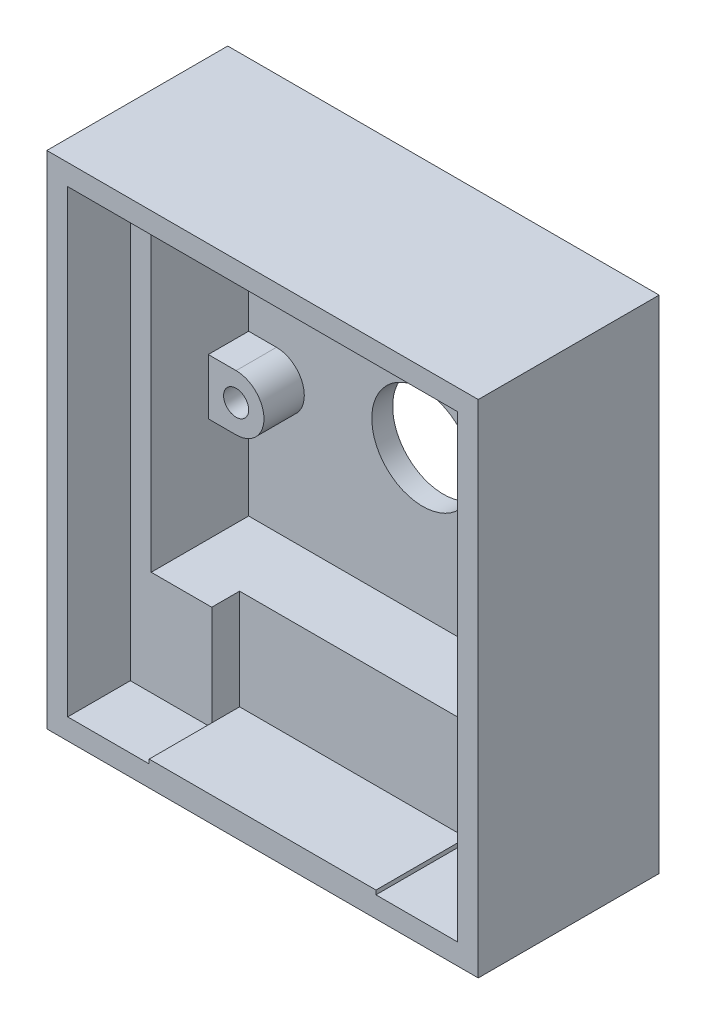
SolidWorks part; units mm, degrees
ref_plane "Alzado" through (0, 0, 0) normal (0, 0, 1) x (1, 0, 0)
ref_plane "Planta" through (0, 0, 0) normal (0, 1, 0) x (1, 0, 0)
ref_plane "Vista lateral" through (0, 0, 0) normal (1, 0, 0) x (0, 0, -1)
sketch "Croquis1" plane through (0, 0, 0) normal (0, 0, 1) x (1, 0, 0)
  line L1 (-4.65, -4.5) -> (4.65, -4.5) construction
  line L2 (-4.65, -4.5) -> (-4.65, 4.5) construction
  line L3 (-4.65, 4.5) -> (4.65, 4.5) construction
  line L4 (4.65, -4.5) -> (4.65, 4.5) construction
  line L5 (-4.65, -4.5) -> (4.65, 4.5) construction
  line L6 (-4.65, 4.5) -> (4.65, -4.5) construction
  line L7 (-12.5, -10.5) -> (12.5, -10.5)
  line L8 (-12.5, -10.5) -> (-12.5, 13.5)
  line L9 (-12.5, 13.5) -> (12.5, 13.5)
  line L10 (12.5, -10.5) -> (12.5, 13.5)
  circle A0 centre (0, 0) radius 3.65
  point P1 (0, 0)
  point P6 (0, 0)
  point P11 (0, 0)
  point P16 (0, 13.5)
  dimension "D6" = 7.3
  dimension "D1" = 25
  dimension "D2" = 9.3
  dimension "D3" = 9
  dimension "D4" = 6
  dimension "D5" = 24
extrude "Saliente-Extruir1" add sketch "Croquis1" along normal blind 1.5
sketch "Croquis4" plane through (0, 0, 0) normal (0, 0, -1) x (-1, 0, 0)
  line L0 (12.5, -10.5) -> (12.5, 13.5)
  line L1 (12.5, 13.5) -> (-12.5, 13.5)
  line L2 (-12.5, 13.5) -> (-12.5, -10.5)
  line L3 (-12.5, -10.5) -> (-15.5, -10.5)
  line L4 (-15.5, -10.5) -> (-15.5, 16.5)
  line L5 (-15.5, 16.5) -> (15.5, 16.5)
  line L6 (15.5, 16.5) -> (15.5, -10.5)
  line L7 (15.5, -10.5) -> (12.5, -10.5)
  dimension "D1" = 3
  dimension "D2" = 3
  dimension "D3" = 3
extrude "Saliente-Extruir7" add sketch "Croquis4" against normal blind 8.5
sketch "Croquis2" plane through (0, 0, 1.5) normal (0, 0, 1) x (1, 0, 0)
  line L2 (-12.5, 13.5) -> (-12.5, -10.5) construction
  line L3 (12.5, 13.5) -> (-12.5, 13.5) construction
  line L4 (-10.5, 9.5) -> (-12.5, 9.5)
  line L5 (-12.5, 13.5) -> (-12.5, -10.5) construction
  line L6 (-12.5, 9.5) -> (-12.5, 13.5)
  line L7 (-12.5, 13.5) -> (-10.5, 13.5)
  line L8 (-10.5, -3) -> (-12.5, -3)
  line L9 (-12.5, -3) -> (-12.5, 1)
  line L10 (-12.5, 1) -> (-10.5, 1)
  arc A0 (-10.5, 9.5) -> (-10.5, 13.5) centre (-10.5, 11.5) ccw
  arc A1 (-10.5, -3) -> (-10.5, 1) centre (-10.5, -1) ccw
  circle A2 centre (-10.5, 11.5) radius 0.9
  circle A3 centre (-10.5, -1) radius 0.9
  dimension "D1" = 4
  dimension "D2" = 1.8
  dimension "D3" = 2
  dimension "D4" = 2
  dimension "D5" = 12.5
extrude "Saliente-Extruir2" add sketch "Croquis2" along normal blind 2.9
mirror "Simetría2" about plane through (0, 0, 0) normal (1, 0, 0) of "Saliente-Extruir2"
sketch "Croquis5" plane through (0, 0, 0) normal (0, 0, -1) x (-1, 0, 0)
  line L0 (12.5, -10.5) -> (-12.5, -10.5) construction
  line L1 (8.15, -10.5) -> (-8.15, -10.5) construction
  line L2 (8.15, -10.5) -> (8.15, -16.2434) construction
  line L3 (8.15, -16.2434) -> (-8.15, -16.2434) construction
  line L4 (-8.15, -10.5) -> (-8.15, -16.2434) construction
  line L5 (-8.15, -10.5) -> (-8.15, -14.15)
  line L6 (-15.5, 16.5) -> (-15.5, -10.5) construction
  line L7 (15.5, -10.5) -> (-15.5, -10.5)
  line L8 (15.5, -10.5) -> (15.5, -19.5)
  line L9 (15.5, -19.5) -> (-15.5, -19.5)
  line L10 (-15.5, -10.5) -> (-15.5, -19.5)
  circle A0 centre (-10.8, -14.15) radius 2.65 construction
  point P6 (0, -10.5)
  point P10 (-10.8, -11.5)
  dimension "D2" = 5.3
  dimension "D1" = 16.3
  dimension "D3" = 1
  dimension "D4" = 9
extrude "Saliente-Extruir8" add sketch "Croquis5" against normal blind 6.5 contours L9 L10 L7 L8
sketch "Croquis6" plane through (0, 0, 6.5) normal (0, 0, 1) x (1, 0, 0)
  circle A0 centre (10.8, -14.15) radius 2.65 construction
  circle A1 centre (10.8, -14.15) radius 2.65
extrude "Cortar-Extruir1" cut sketch "Croquis6" against normal blind 6.5
sketch "Croquis7" plane through (0, 0, 6.5) normal (0, 0, 1) x (1, 0, 0)
  line L0 (-15.5, -19.5) -> (15.5, -19.5) construction
  line L1 (-15.5, -10.5) -> (-8.15, -10.5)
  line L2 (-15.5, -10.5) -> (-15.5, -19.5)
  line L3 (-15.5, -19.5) -> (-8.15, -19.5)
  line L4 (-8.15, -10.5) -> (-8.15, -17.7)
  line L5 (-15.5, -10.5) -> (15.5, -10.5) construction
  line L6 (15.5, -19.5) -> (8.15, -19.5)
  line L7 (15.5, -19.5) -> (15.5, -10.5)
  line L8 (15.5, -10.5) -> (8.15, -10.5)
  line L9 (8.15, -17.7) -> (8.15, -14.7688)
  line L10 (-8.15, -10.5) -> (-8.15, -16.2434) construction
  line L11 (8.15, -10.5) -> (8.15, -16.2434) construction
  line L12 (8.15, -13.3581) -> (8.2711, -13.3581)
  line L13 (8.15, -14.7688) -> (8.2233, -14.7688)
  line L14 (8.15, -13.3581) -> (8.15, -10.5)
  line L16 (-8.15, -19.5) -> (8.15, -19.5)
  line L18 (-8.15, -17.7) -> (8.15, -17.7)
  circle A0 centre (10.8, -14.15) radius 2.65 construction
  arc A1 (8.2233, -14.7688) -> (8.2711, -13.3581) centre (10.8, -14.15) ccw
  dimension "D1" = 1.8
extrude "Saliente-Extruir9" add sketch "Croquis7" along normal up to surface (2 mm away) up to face at (0, 2.25, 8.5)
sketch "Croquis8" plane through (0, 0, 8.5) normal (0, 0, 1) x (1, 0, 0)
  line L0 (8.15, -17.7) -> (-8.15, -17.7) construction
  line L1 (-15.5, -19.5) -> (15.5, -19.5)
  line L2 (-15.5, -19.5) -> (-15.5, 16.5)
  line L3 (-15.5, 16.5) -> (15.5, 16.5)
  line L4 (15.5, -19.5) -> (15.5, 16.5)
  line L5 (-14, 15) -> (14, 15)
  line L6 (-14, 15) -> (-14, -18)
  line L7 (-14, -18) -> (-8.15, -18)
  line L8 (14, 15) -> (14, -18)
  line L10 (-8.15, -18) -> (-8.15, -17.7)
  line L11 (-8.15, -17.7) -> (8.15, -17.7)
  line L12 (8.15, -18) -> (8.15, -17.7)
  line L13 (8.15, -14.7688) -> (8.15, -17.7) construction
  line L14 (-8.15, -17.7) -> (-8.15, -10.5) construction
  line L15 (8.15, -18) -> (14, -18)
  dimension "D1" = 1.5
  dimension "D2" = 1.5
  dimension "D3" = 1.5
  dimension "D4" = 1.5
extrude "Saliente-Extruir10" add sketch "Croquis8" along normal up to surface (4.5 mm away)
sketch "Croquis9" plane through (0, 0, 8.5) normal (0, 0, 1) x (1, 0, 0)
  line L4 (14, -18) -> (8.15, -18)
  line L5 (14, -18) -> (14, -10.5)
  line L6 (14, -10.5) -> (8.15, -10.5)
  line L7 (8.15, -18) -> (8.15, -10.5)
extrude "Cortar-Extruir3" cut sketch "Croquis9" against normal up to surface (2 mm away) up to face at (4.0873, -14.0813, 6.5)
